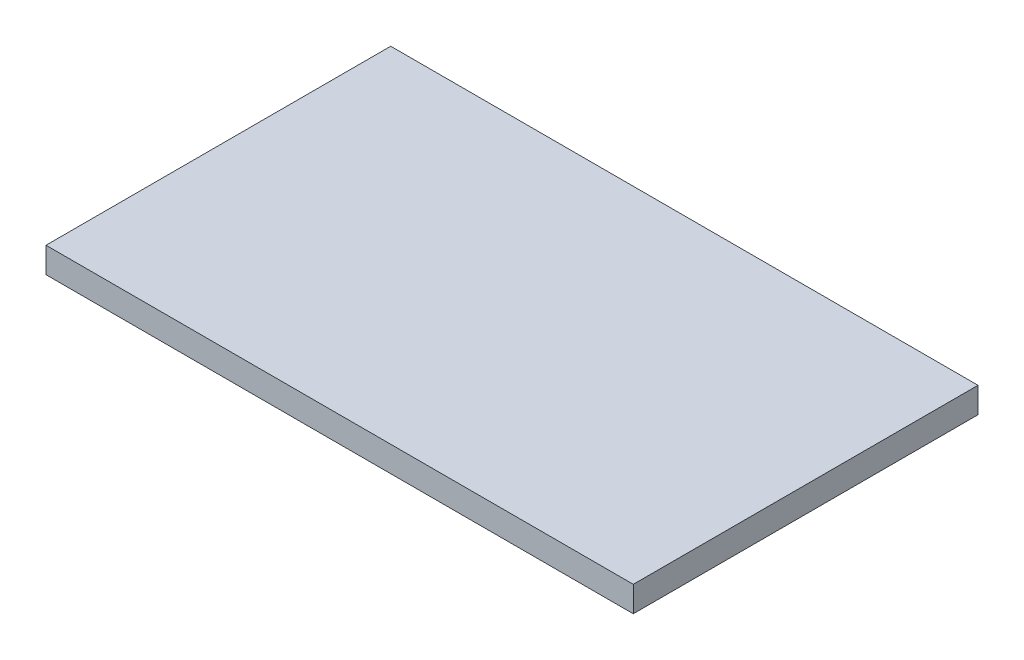
SolidWorks part; units mm, degrees
material "Acrylic (Medium-high impact)"
ref_plane "Front Plane" through (0, 0, 0) normal (0, 0, 1) x (1, 0, 0)
ref_plane "Top Plane" through (0, 0, 0) normal (0, 1, 0) x (1, 0, 0)
ref_plane "Right Plane" through (0, 0, 0) normal (1, 0, 0) x (0, 0, -1)
sketch "Sketch1" plane through (0, 0, 0) normal (0, 1, 0) x (1, 0, 0)
  line L1 (-36.5125, -21.4312) -> (36.5125, -21.4312)
  line L2 (-36.5125, -21.4312) -> (-36.5125, 21.4312)
  line L3 (-36.5125, 21.4312) -> (36.5125, 21.4312)
  line L4 (36.5125, -21.4312) -> (36.5125, 21.4312)
  line L5 (-36.5125, -21.4312) -> (36.5125, 21.4312) construction
  line L6 (-36.5125, 21.4312) -> (36.5125, -21.4312) construction
  point P0 (0, 0)
  dimension "D1" = 42.8625
  dimension "D2" = 73.025
extrude "Boss-Extrude1" add sketch "Sketch1" along normal blind 3.175
